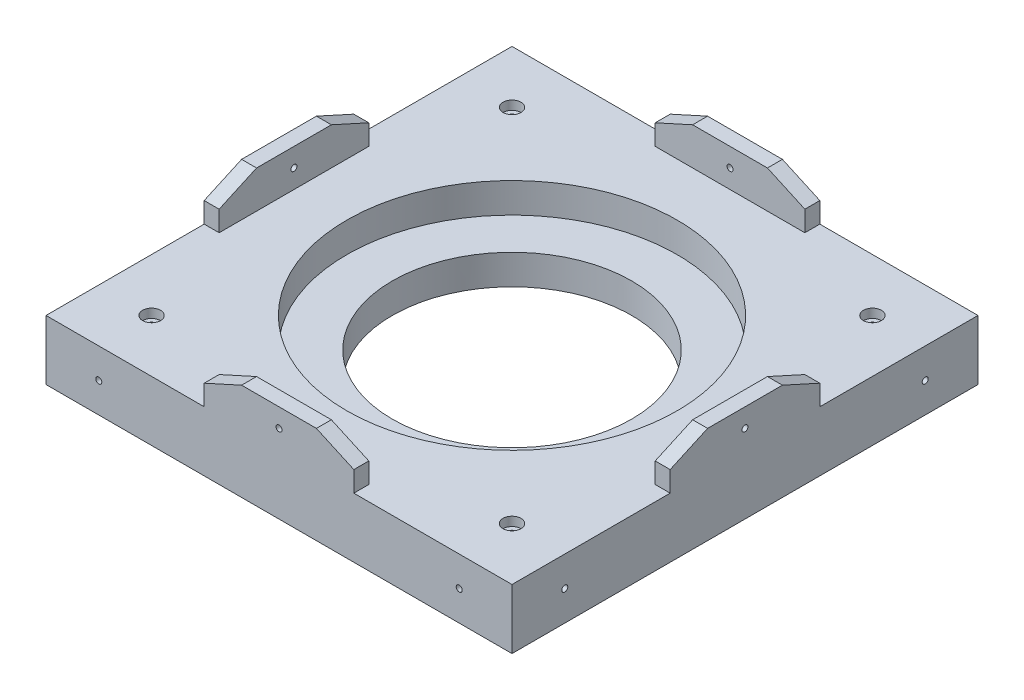
SolidWorks part; units mm, degrees
ref_plane "Front Plane" through (0, 0, 0) normal (0, 0, 1) x (1, 0, 0)
ref_plane "Top Plane" through (0, 0, 0) normal (0, 1, 0) x (1, 0, 0)
ref_plane "Right Plane" through (0, 0, 0) normal (1, 0, 0) x (0, 0, -1)
sketch "Sketch1" plane through (0, 0, 0) normal (0, 1, 0) x (1, 0, 0)
  line L0 (77.4608, -75.0982) -> (77.4608, 74.5774)
  line L1 (74.4472, 77.591) -> (-75.2284, 77.591)
  line L2 (-78.242, 74.5774) -> (-78.242, -75.0982)
  line L3 (-75.2284, -78.1118) -> (74.4472, -78.1118)
  line L4 (-78.242, -0.2604) -> (77.4608, -0.2604) construction
  line L5 (-0.3906, 77.591) -> (-0.3906, -78.1118) construction
  circle A0 centre (-60.6043, -60.4741) radius 1.5
  circle A1 centre (-60.6043, 59.9534) radius 1.5
  circle A2 centre (59.8232, 59.9534) radius 1.5
  circle A3 centre (59.8232, -60.4741) radius 1.5
  arc A4 (77.4608, 74.5774) -> (74.4472, 77.591) centre (74.4472, 74.5774) ccw
  arc A5 (-75.2284, 77.591) -> (-78.242, 74.5774) centre (-75.2284, 74.5774) ccw
  arc A6 (-78.242, -75.0982) -> (-75.2284, -78.1118) centre (-75.2284, -75.0982) ccw
  arc A7 (74.4472, -78.1118) -> (77.4608, -75.0982) centre (74.4472, -75.0982) ccw
  circle A10 centre (-0.3906, -0.2604) radius 73
  dimension "D2" = 146
  dimension "D3" = 3
  dimension "D1" = 155.7028
extrude "Boss-Extrude1" add sketch "Sketch1" along normal blind 20
sketch "Sketch7" plane through (0, 20, 0) normal (0, 1, 0) x (1, 0, 0)
  circle A0 centre (-0.3906, -0.2604) radius 73 construction
  circle A1 centre (-0.3906, -0.2604) radius 73
  circle A2 centre (-0.3906, -0.2604) radius 52.25
  dimension "D1" = 104.5
extrude "Boss-Extrude2" add sketch "Sketch7" against normal blind 10
sketch "Sketch8" plane through (0, 10, 0) normal (0, -1, 0) x (1, 0, 0)
  circle A1 centre (-0.3906, 0.2604) radius 73
  circle A2 centre (-0.3906, 0.2604) radius 73
  dimension "D1" = 0
extrude "Boss-Extrude3" add sketch "Sketch8" along normal up to surface (10 mm away) up to face at (-0.3906, 0, 0.2604)
sketch "Sketch9" plane through (0, 20, 0) normal (0, 1, 0) x (1, 0, 0)
  line L1 (-78.242, 77.591) -> (77.4608, 77.591)
  line L2 (-78.242, 77.591) -> (-78.242, -78.1118)
  line L3 (-78.242, -78.1118) -> (77.4608, -78.1118)
  line L4 (77.4608, 77.591) -> (77.4608, -78.1118)
  line L10 (77.4608, -75.0982) -> (77.4608, 74.5774)
  line L11 (74.4472, 77.591) -> (-75.2284, 77.591)
  line L12 (-78.242, 74.5774) -> (-78.242, -75.0982)
  line L13 (-75.2284, -78.1118) -> (74.4472, -78.1118)
  line L14 (77.4608, -75.0982) -> (77.4608, 74.5774)
  line L15 (74.4472, 77.591) -> (-75.2284, 77.591)
  line L16 (-78.242, 74.5774) -> (-78.242, -75.0982)
  line L17 (-75.2284, -78.1118) -> (74.4472, -78.1118)
  arc A6 (74.4472, -78.1118) -> (77.4608, -75.0982) centre (74.4472, -75.0982) ccw
  arc A7 (77.4608, 74.5774) -> (74.4472, 77.591) centre (74.4472, 74.5774) ccw
  arc A8 (-75.2284, 77.591) -> (-78.242, 74.5774) centre (-75.2284, 74.5774) ccw
  arc A9 (-78.242, -75.0982) -> (-75.2284, -78.1118) centre (-75.2284, -75.0982) ccw
  arc A10 (74.4472, -78.1118) -> (77.4608, -75.0982) centre (74.4472, -75.0982) ccw
  arc A11 (77.4608, 74.5774) -> (74.4472, 77.591) centre (74.4472, 74.5774) ccw
  arc A12 (-75.2284, 77.591) -> (-78.242, 74.5774) centre (-75.2284, 74.5774) ccw
  arc A13 (-78.242, -75.0982) -> (-75.2284, -78.1118) centre (-75.2284, -75.0982) ccw
  arc M12 (74.4472, -78.1118) -> (77.4608, -75.0982) centre (74.4472, -75.0982) ccw
  arc M14 (77.4608, 74.5774) -> (74.4472, 77.591) centre (74.4472, 74.5774) ccw
  arc M16 (-75.2284, 77.591) -> (-78.242, 74.5774) centre (-75.2284, 74.5774) ccw
  arc M18 (-78.242, -75.0982) -> (-75.2284, -78.1118) centre (-75.2284, -75.0982) ccw
  dimension "D2" = 0
extrude "Boss-Extrude4" add sketch "Sketch9" against normal up to surface (20 mm away) contours L2 L3 M18 | L4 L3 M12 | L4 L1 M14 | L1 L2 M16 up to face at (-0.3906, 0, 0.2604)
sketch "Sketch10" plane through (0, 20, 0) normal (0, 1, 0) x (1, 0, 0)
  circle A0 centre (-0.3906, -0.2604) radius 52.25 construction
  circle A1 centre (-0.3906, -0.2604) radius 52.25
  circle A2 centre (-0.3906, -0.2604) radius 55.2
  dimension "D1" = 110.4
extrude "Cut-Extrude1" cut sketch "Sketch10" against normal blind 10
sketch "Sketch11" plane through (0, 20, 0) normal (0, 1, 0) x (1, 0, 0)
  circle A0 centre (-0.3906, -0.2604) radius 40
  dimension "D2" = 80
extrude "Cut-Extrude2" cut sketch "Sketch11" against normal blind 50
sketch "Sketch12" plane through (0, 20, 0) normal (0, 1, 0) x (1, 0, 0)
  circle A0 centre (59.8232, 59.9534) radius 1.5 construction
  circle A1 centre (-60.6043, 59.9534) radius 1.5 construction
  circle A2 centre (-60.6043, -60.4741) radius 1.5 construction
  circle A3 centre (59.8232, -60.4741) radius 1.5 construction
  circle A4 centre (59.8232, 59.9534) radius 1.5
  circle A5 centre (-60.6043, 59.9534) radius 1.5
  circle A6 centre (-60.6043, -60.4741) radius 1.5
  circle A7 centre (59.8232, -60.4741) radius 1.5
  circle A8 centre (59.8232, 59.9534) radius 3
  circle A9 centre (-60.6043, 59.9534) radius 3
  circle A10 centre (-60.6043, -60.4741) radius 3
  circle A11 centre (59.8232, -60.4741) radius 3
  dimension "D1" = 1.5
extrude "Cut-Extrude3" cut sketch "Sketch12" against normal blind 3
sketch "Sketch13" plane through (-78.242, 0, 0) normal (-1, 0, 0) x (0, 0, 1)
  line L0 (-77.591, 20) -> (78.1118, 20) construction
  line L1 (-24.7396, 26.8236) -> (-24.7396, 32.4949) construction
  line L2 (-24.7396, 26.8236) -> (25.2604, 26.8236)
  line L3 (-24.7396, 26.8236) -> (-24.7396, 13.1764)
  line L4 (-24.7396, 13.1764) -> (25.2604, 13.1764)
  line L5 (25.2604, 26.8236) -> (25.2604, 13.1764)
  line L6 (0.2604, 13.1764) -> (0.2604, 26.8236) construction
  line L7 (-24.7396, 20) -> (25.2604, 20) construction
  line L8 (-24.7396, 32.4949) -> (0.2604, 32.4949) construction
  line L9 (0.2604, 32.4949) -> (0.2604, 27.9256) construction
  line L10 (0.2604, 32.4949) -> (25.2604, 32.4949) construction
  line L11 (-12.2396, 32.4949) -> (-24.7396, 26.8236)
  line L12 (-12.2396, 32.4949) -> (12.7604, 32.4949)
  line L13 (12.7604, 32.4949) -> (25.2604, 26.8236)
  point P0 (0.2604, 20)
  point P1 (0.2604, 20)
  line M4 (78.1118, 20) -> (-77.591, 20)
  dimension "D1" = 50
extrude "Boss-Extrude5" add sketch "Sketch13" against normal blind 5 contours L5 L2 L3 M4 | L13 L12 L11 L2
sketch "Sketch14" plane through (77.4608, 0, 0) normal (1, 0, 0) x (0, 0, -1)
  line L6 (-25.2604, 26.8236) -> (-25.2604, 20)
  line L7 (-25.2604, 20) -> (24.7396, 20)
  line L8 (24.7396, 20) -> (24.7396, 26.8236)
  line L9 (24.7396, 26.8236) -> (12.2396, 32.4949)
  line L10 (12.2396, 32.4949) -> (-12.7604, 32.4949)
  line L11 (-12.7604, 32.4949) -> (-25.2604, 26.8236)
  line L12 (-25.2604, 26.8236) -> (-25.2604, 20)
  line L13 (-25.2604, 20) -> (24.7396, 20)
  line L14 (24.7396, 20) -> (24.7396, 26.8236)
  line L15 (24.7396, 26.8236) -> (12.2396, 32.4949)
  line L16 (12.2396, 32.4949) -> (-12.7604, 32.4949)
  line L17 (-12.7604, 32.4949) -> (-25.2604, 26.8236)
  dimension "D1" = 0
extrude "Boss-Extrude6" add sketch "Sketch14" against normal blind 5
sketch "Sketch17" plane through (0, 0, -77.591) normal (0, 0, -1) x (-1, 0, 0)
  line L0 (-77.4608, 0) -> (78.242, 0)
  line L1 (78.242, 0) -> (78.242, 20)
  line L2 (78.242, 20) -> (25.3906, 20)
  line L3 (25.3906, 20) -> (25.3906, 26.8236)
  line L4 (25.3906, 26.8236) -> (12.8906, 32.4949)
  line L5 (12.8906, 32.4949) -> (-12.1094, 32.4949)
  line L6 (-12.1094, 32.4949) -> (-24.6094, 26.8236)
  line L7 (-24.6094, 26.8236) -> (-24.6094, 20)
  line L8 (-24.6094, 20) -> (-77.4608, 20)
  line L9 (-77.4608, 20) -> (-77.4608, 0)
  point P10 (-77.4608, 0)
extrude "Boss-Extrude7" add sketch "Sketch17" against normal blind 5
sketch "Sketch18" plane through (0, 0, 78.1118) normal (0, 0, 1) x (1, 0, 0)
  line L6 (-25.3906, 20) -> (24.6094, 20)
  line L7 (24.6094, 20) -> (24.6094, 26.8236)
  line L8 (24.6094, 26.8236) -> (12.1094, 32.4949)
  line L9 (12.1094, 32.4949) -> (-12.8906, 32.4949)
  line L10 (-12.8906, 32.4949) -> (-25.3906, 26.8236)
  line L11 (-25.3906, 26.8236) -> (-25.3906, 20)
  line L12 (-25.3906, 20) -> (24.6094, 20)
  line L13 (24.6094, 20) -> (24.6094, 26.8236)
  line L14 (24.6094, 26.8236) -> (12.1094, 32.4949)
  line L15 (12.1094, 32.4949) -> (-12.8906, 32.4949)
  line L16 (-12.8906, 32.4949) -> (-25.3906, 26.8236)
  line L17 (-25.3906, 26.8236) -> (-25.3906, 20)
  dimension "D1" = 0
extrude "Boss-Extrude8" add sketch "Sketch18" against normal blind 5
sketch "Sketch19" plane through (-78.242, 0, 0) normal (-1, 0, 0) x (0, 0, 1)
  line L0 (-12.2396, 32.4949) -> (12.7604, 32.4949) construction
  line L2 (-80.091, -68) -> (80.6118, -68)
  line L4 (80.6118, 20) -> (25.2604, 20)
  line L5 (25.2604, 20) -> (25.2604, 26.8236)
  line L6 (25.2604, 26.8236) -> (12.7604, 32.4949)
  line L7 (12.7604, 32.4949) -> (-12.2396, 32.4949)
  line L8 (-12.2396, 32.4949) -> (-24.7396, 26.8236)
  line L9 (-24.7396, 26.8236) -> (-24.7396, 20)
  line L10 (-24.7396, 20) -> (-80.091, 20)
  circle A0 centre (60.4741, 10) radius 1.5
  circle A1 centre (-59.9534, 10) radius 1.5
  circle A2 centre (0.2604, 26.2475) radius 1.5
  point P0 (0.2604, 32.4949)
  point P19 (0.2604, 32.4949)
extrude "Cut-Extrude4" cut sketch "Sketch19" against normal up to surface (5 mm away) contours A2 | A0 | A1 up to face at (-73.242, 26.4395, 0.2604)
sketch "Sketch20" plane through (77.4608, 0, 0) normal (1, 0, 0) x (0, 0, -1)
  circle A0 centre (-60.4741, 10) radius 1.5 construction
  circle A1 centre (59.9534, 10) radius 1.5 construction
  circle A2 centre (-0.2604, 26.2475) radius 1.5 construction
  circle A3 centre (-60.4741, 10) radius 1.5
  circle A4 centre (59.9534, 10) radius 1.5
  circle A5 centre (-0.2604, 26.2475) radius 1.5
extrude "Cut-Extrude5" cut sketch "Sketch20" against normal up to surface (5 mm away) up to face at (72.4608, 26.4395, 0.2604)
sketch "Sketch21" plane through (0, 0, -77.591) normal (0, 0, -1) x (-1, 0, 0)
  line L0 (12.8906, 32.4949) -> (-12.1094, 32.4949) construction
  line L2 (-79.9608, -68) -> (80.742, -68)
  line L3 (80.742, -68) -> (80.742, 20)
  line L4 (80.742, 20) -> (25.3906, 20)
  line L5 (25.3906, 20) -> (25.3906, 26.8236)
  line L6 (25.3906, 26.8236) -> (12.8906, 32.4949)
  line L7 (12.8906, 32.4949) -> (-12.1094, 32.4949)
  line L8 (-12.1094, 32.4949) -> (-24.6094, 26.8236)
  line L9 (-24.6094, 26.8236) -> (-24.6094, 20)
  line L10 (-24.6094, 20) -> (-79.9608, 20)
  circle A0 centre (60.6043, 10) radius 1.5
  circle A1 centre (-59.8232, 10) radius 1.5
  circle A2 centre (0.3906, 26.2475) radius 1.5
  point P0 (0.3906, 32.4949)
  point P19 (0.3906, 32.4949)
extrude "Cut-Extrude6" cut sketch "Sketch21" against normal up to surface (5 mm away) contours A1 | A2 | A0 up to face at (-0.3906, 26.4395, -72.591)
sketch "Sketch22" plane through (0, 0, 78.1118) normal (0, 0, 1) x (1, 0, 0)
  line L0 (12.1094, 32.4949) -> (-12.8906, 32.4949) construction
  line L2 (-80.742, -68) -> (79.9608, -68)
  line L3 (79.9608, -68) -> (79.9608, 20)
  line L4 (79.9608, 20) -> (24.6094, 20)
  line L5 (24.6094, 20) -> (24.6094, 26.8236)
  line L6 (24.6094, 26.8236) -> (12.1094, 32.4949)
  line L7 (12.1094, 32.4949) -> (-12.8906, 32.4949)
  line L8 (-12.8906, 32.4949) -> (-25.3906, 26.8236)
  line L9 (-25.3906, 26.8236) -> (-25.3906, 20)
  line L10 (-25.3906, 20) -> (-80.742, 20)
  circle A0 centre (59.8232, 10) radius 1.5
  circle A1 centre (-60.6043, 10) radius 1.5
  circle A2 centre (-0.3906, 26.2475) radius 1.5
  point P0 (-0.3906, 32.4949)
extrude "Cut-Extrude7" cut sketch "Sketch22" against normal up to surface (5 mm away) contours A0 | A2 | A1 up to face at (-0.3906, 26.4395, 73.1118)
sketch "Sketch23" plane through (-78.242, 0, 0) normal (-1, 0, 0) x (0, 0, 1)
  circle A0 centre (60.4741, 10) radius 1.5 construction
  circle A1 centre (-59.9534, 10) radius 1.5 construction
  circle A2 centre (0.2604, 26.2475) radius 1.5 construction
  circle A3 centre (60.4741, 10) radius 1.5
  circle A4 centre (-59.9534, 10) radius 1.5
  circle A5 centre (0.2604, 26.2475) radius 1.5
  circle A6 centre (60.4741, 10) radius 1
  circle A7 centre (-59.9534, 10) radius 1
  circle A8 centre (0.2604, 26.2475) radius 1
  dimension "D1" = 0.5
extrude "Boss-Extrude9" add sketch "Sketch23" against normal blind 5
sketch "Sketch24" plane through (0, 0, 78.1118) normal (0, 0, 1) x (1, 0, 0)
  circle A0 centre (-60.6043, 10) radius 1
  circle A1 centre (-60.6043, 10) radius 1.5
  circle A2 centre (-60.6043, 10) radius 1.5
  circle A3 centre (-0.3906, 26.2475) radius 1.5
  circle A4 centre (-0.3906, 26.2475) radius 1.5
  circle A5 centre (59.8232, 10) radius 1.5
  circle A6 centre (59.8232, 10) radius 1.5
  circle A7 centre (-0.3906, 26.2475) radius 1
  circle A8 centre (59.8232, 10) radius 1
  dimension "D1" = 0
  dimension "D2" = 0
  dimension "D3" = 0
  dimension "D4" = 0.5
extrude "Boss-Extrude10" add sketch "Sketch24" against normal blind 5
sketch "Sketch25" plane through (77.4608, 0, 0) normal (1, 0, 0) x (0, 0, -1)
  circle A0 centre (-60.4741, 10) radius 1.5 construction
  circle A1 centre (59.9534, 10) radius 1.5 construction
  circle A2 centre (-0.2604, 26.2475) radius 1.5 construction
  circle A3 centre (-60.4741, 10) radius 1.5
  circle A4 centre (59.9534, 10) radius 1.5
  circle A5 centre (-0.2604, 26.2475) radius 1.5
  circle A6 centre (-60.4741, 10) radius 1
  circle A7 centre (59.9534, 10) radius 1
  circle A8 centre (-0.2604, 26.2475) radius 1
  dimension "D1" = 0.5
extrude "Boss-Extrude11" add sketch "Sketch25" against normal blind 5
sketch "Sketch26" plane through (0, 0, -77.591) normal (0, 0, -1) x (-1, 0, 0)
  circle A0 centre (-59.8232, 10) radius 1.5 construction
  circle A1 centre (60.6043, 10) radius 1.5 construction
  circle A2 centre (0.3906, 26.2475) radius 1.5 construction
  circle A3 centre (-59.8232, 10) radius 1.5
  circle A4 centre (60.6043, 10) radius 1.5
  circle A5 centre (0.3906, 26.2475) radius 1.5
  circle A6 centre (-59.8232, 10) radius 1
  circle A7 centre (60.6043, 10) radius 1
  circle A8 centre (0.3906, 26.2475) radius 1
  dimension "D1" = 0.5
extrude "Boss-Extrude12" add sketch "Sketch26" against normal blind 5
